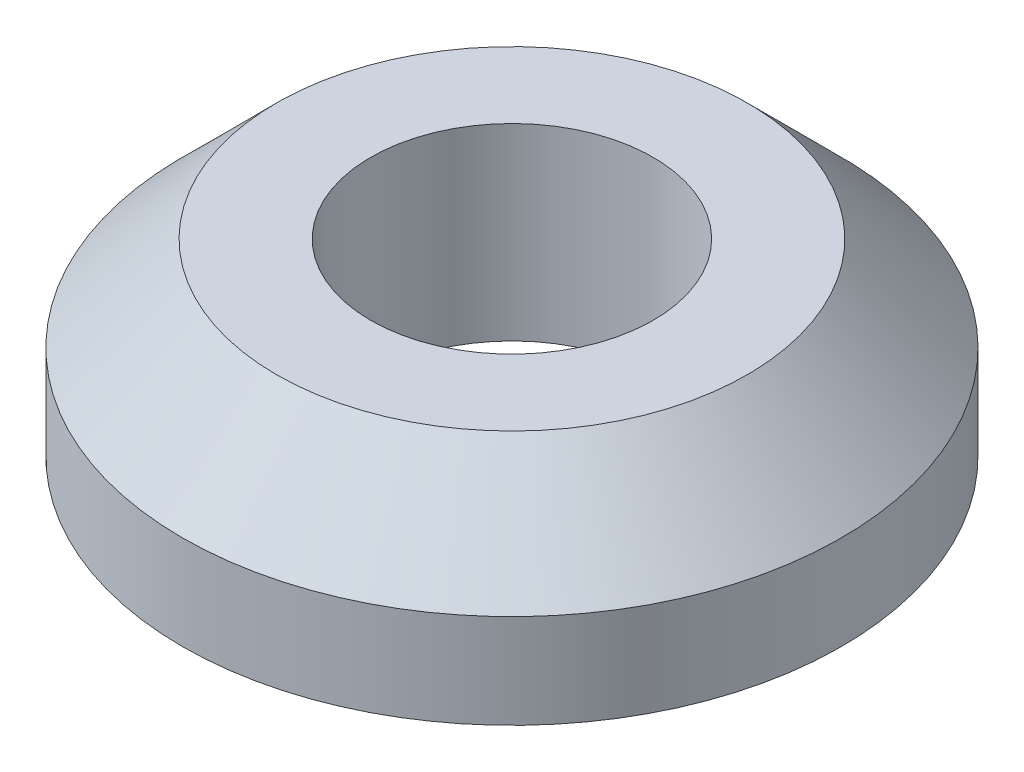
SolidWorks part; units mm, degrees
ref_plane "Front Plane" through (0, 0, 0) normal (0, 0, 1) x (1, 0, 0)
ref_plane "Top Plane" through (0, 0, 0) normal (0, 1, 0) x (1, 0, 0)
ref_plane "Right Plane" through (0, 0, 0) normal (1, 0, 0) x (0, 0, -1)
sketch "Sketch1" plane through (0, 0, 0) normal (0, 1, 0) x (1, 0, 0)
  circle A0 centre (0, 0) radius 3.5
  dimension "D1" = 7
extrude "Boss-Extrude1" add sketch "Sketch1" along normal blind 2
sketch "Sketch2" plane through (0, 2, 0) normal (0, 1, 0) x (1, 0, 0)
  circle A0 centre (0, 0) radius 1.5
  dimension "D1" = 3
extrude "Cut-Extrude1" cut sketch "Sketch2" against normal blind 2
chamfer "Chamfer1" distance 1 angle 45 1 edges at (0, 2, 3.5)
